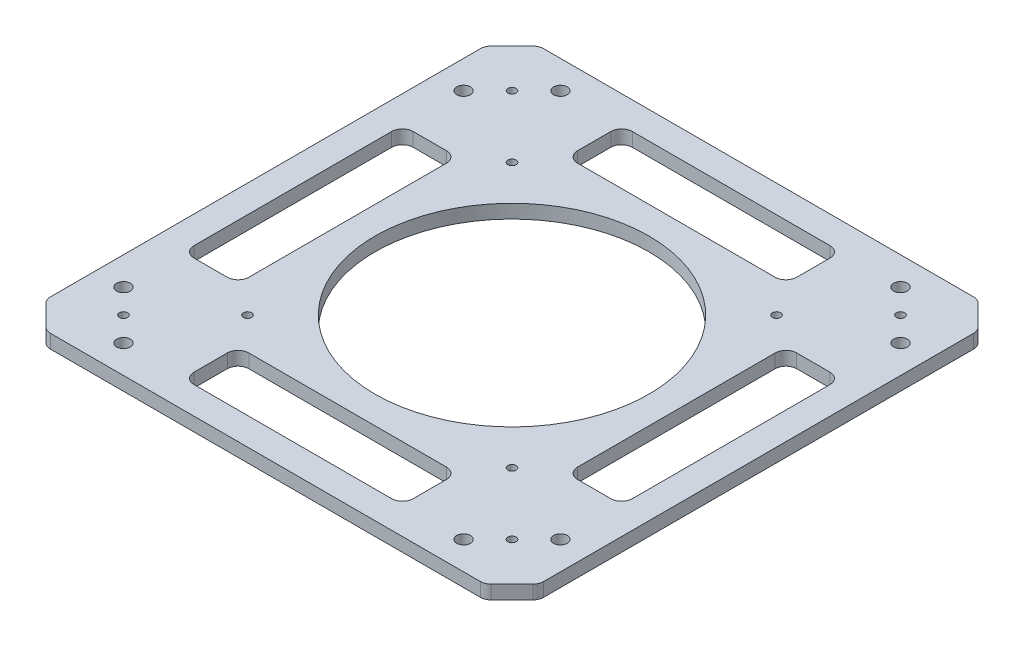
SolidWorks part; units mm, degrees
material "Hexcel AS4C (3000 Filaments)"
ref_plane "Front Plane" through (0, 0, 0) normal (0, 0, 1) x (1, 0, 0)
ref_plane "Top Plane" through (0, 0, 0) normal (0, 1, 0) x (1, 0, 0)
ref_plane "Right Plane" through (0, 0, 0) normal (1, 0, 0) x (0, 0, -1)
sketch "Sketch1" plane through (0, 0, 0) normal (0, 1, 0) x (1, 0, 0)
  line L0 (0, 0) -> (656.8243, 0) construction
  line L1 (0, 0) -> (0, 507.0819) construction
  line L2 (-203.454, 228.5987) -> (203.454, 228.5987)
  line L3 (203.454, 228.5987) -> (228.5987, 203.454)
  line L4 (228.5987, 203.454) -> (228.5987, -203.454)
  line L5 (203.454, -228.5987) -> (228.5987, -203.454)
  line L6 (-203.454, -228.5987) -> (203.454, -228.5987)
  line L7 (-203.454, -228.5987) -> (-228.5987, -203.454)
  line L8 (-228.5987, 203.454) -> (-228.5987, -203.454)
  line L9 (-203.454, 228.5987) -> (-228.5987, 203.454)
  point P4 (0, 0)
  point P11 (228.5987, 0)
  point P14 (0, -228.5987)
  point P17 (0, 228.5987)
  dimension "D1" = 203.454
  dimension "D2" = 35.56
  dimension "D3" = 45
extrude "Boss-Extrude1" add sketch "Sketch1" along normal blind 12.7
sketch "Sketch2" plane through (0, 12.7, 0) normal (0, 1, 0) x (1, 0, 0)
  line L0 (202.556, 157.6547) -> (221.4375, 176.5362) construction
  line L1 (0, 0) -> (0, 320.9857) construction
  line L2 (0, 0) -> (464.4972, 0) construction
  line L3 (122.6317, 122.6317) -> (180.1053, 180.1053) construction
  line L4 (118.1416, 127.1218) -> (175.6152, 184.5955)
  line L5 (127.1218, 118.1416) -> (184.5955, 175.6152)
  line L7 (-122.6317, 122.6317) -> (-180.1053, 180.1053) construction
  line L8 (-118.1416, 127.1218) -> (-175.6152, 184.5955)
  line L9 (-127.1218, 118.1416) -> (-184.5955, 175.6152)
  line L10 (-122.6317, -122.6317) -> (-180.1053, -180.1053) construction
  line L11 (-118.1416, -127.1218) -> (-175.6152, -184.5955)
  line L12 (-127.1218, -118.1416) -> (-184.5955, -175.6152)
  line L13 (122.6317, -122.6317) -> (180.1053, -180.1053) construction
  line L14 (118.1416, -127.1218) -> (175.6152, -184.5955)
  line L15 (127.1218, -118.1416) -> (184.5955, -175.6152)
  line L16 (0, 0) -> (244.2076, 244.2076) construction
  line L18 (228.5987, 203.454) -> (203.454, 228.5987) construction
  line L19 (180.1053, 180.1053) -> (202.556, 157.6547) construction
  arc A0 (118.1416, 127.1218) -> (127.1218, 118.1416) centre (122.6317, 122.6317) ccw
  arc A1 (184.5955, 175.6152) -> (175.6152, 184.5955) centre (180.1053, 180.1053) ccw
  arc A2 (-118.1416, 127.1218) -> (-127.1218, 118.1416) centre (-122.6317, 122.6317) cw
  arc A3 (-184.5955, 175.6152) -> (-175.6152, 184.5955) centre (-180.1053, 180.1053) cw
  arc A4 (-118.1416, -127.1218) -> (-127.1218, -118.1416) centre (-122.6317, -122.6317) ccw
  arc A5 (-184.5955, -175.6152) -> (-175.6152, -184.5955) centre (-180.1053, -180.1053) ccw
  arc A6 (118.1416, -127.1218) -> (127.1218, -118.1416) centre (122.6317, -122.6317) cw
  arc A7 (184.5955, -175.6152) -> (175.6152, -184.5955) centre (180.1053, -180.1053) cw
  circle A8 centre (202.556, 157.6547) radius 6.35
  circle A9 centre (157.6547, 202.556) radius 6.35
  circle A25 centre (-157.6547, 202.556) radius 6.35
  circle A32 centre (-202.556, 157.6547) radius 6.35
  circle A39 centre (-157.6547, -202.556) radius 6.35
  circle A47 centre (-202.556, -157.6547) radius 6.35
  circle A53 centre (157.6547, -202.556) radius 6.35
  circle A57 centre (202.556, -157.6547) radius 6.35
  circle A64 centre (0, 0) radius 127
  circle A73 centre (180.1053, 180.1053) radius 3.81
  circle A74 centre (122.6317, 122.6317) radius 3.81
  circle A75 centre (-180.1053, 180.1053) radius 3.81
  circle A76 centre (-122.6317, 122.6317) radius 3.81
  circle A77 centre (180.1053, -180.1053) radius 3.81
  circle A78 centre (122.6317, -122.6317) radius 3.81
  circle A79 centre (-122.6317, -122.6317) radius 3.81
  circle A80 centre (-180.1053, -180.1053) radius 3.81
  point P7 (151.3685, 151.3685)
  point P21 (-151.3685, 151.3685)
  point P28 (-151.3685, -151.3685)
  point P35 (151.3685, -151.3685)
  point P56 (202.556, 157.6547)
  dimension "D2" = 6.35
  dimension "D5" = 31.75
  dimension "D6" = 12.7
  dimension "D7" = 302.737
  dimension "D8" = 2.54
  dimension "D10" = 254
  dimension "D9" = 2.54
  dimension "D1" = 45
  dimension "D3" = 40.64
  dimension "D4" = 50.8
extrude "Cut-Extrude1" cut sketch "Sketch2" against normal through all both and the other way through all contours A25 | A32 | A47 | A57 | A9 | A8 | A78 | A77 | A79 | A80 | A75 | A76 | A73 | A64 | A74
sketch "Sketch3" plane through (0, 12.7, 0) normal (0, 1, 0) x (1, 0, 0)
  line L0 (0, 0) -> (320.2964, 0) construction
  line L1 (0, 0) -> (0, 272.5431) construction
  line L2 (228.5987, -203.454) -> (228.5987, 203.454) construction
  line L5 (152.3987, -101.6) -> (203.1987, -101.6)
  line L6 (152.3987, -101.6) -> (152.3987, 101.6)
  line L7 (152.3987, 101.6) -> (203.1987, 101.6)
  line L8 (203.1987, -101.6) -> (203.1987, 101.6)
  line L9 (152.3987, -101.6) -> (203.1987, 101.6) construction
  line L10 (152.3987, 101.6) -> (203.1987, -101.6) construction
  line L11 (101.6, -152.3987) -> (101.6, -203.1987)
  line L12 (-101.6, -152.3987) -> (101.6, -152.3987)
  line L13 (-101.6, -203.1987) -> (101.6, -203.1987)
  line L14 (-101.6, -152.3987) -> (-101.6, -203.1987)
  line L15 (-152.3987, -101.6) -> (-203.1987, -101.6)
  line L16 (-152.3987, 101.6) -> (-152.3987, -101.6)
  line L17 (-203.1987, 101.6) -> (-203.1987, -101.6)
  line L18 (-152.3987, 101.6) -> (-203.1987, 101.6)
  line L19 (-101.6, 152.3987) -> (-101.6, 203.1987)
  line L20 (101.6, 152.3987) -> (-101.6, 152.3987)
  line L21 (101.6, 203.1987) -> (-101.6, 203.1987)
  line L22 (101.6, 152.3987) -> (101.6, 203.1987)
  point P3 (177.7987, 0)
  point P26 (0, 0)
  dimension "D1" = 25.4
  dimension "D2" = 101.6
  dimension "D3" = 50.8
  dimension "D4" = 4
extrude "Cut-Extrude2" cut sketch "Sketch3" against normal through all both and the other way through all
fillet "Fillet1" radius 10 8 edges at (-228.5987, 6.35, 203.454) (-203.454, 6.35, 228.5987) (203.454, 6.35, 228.5987) (228.5987, 6.35, 203.454) (228.5987, 6.35, -203.454) (203.454, 6.35, -228.5987) (-203.454, 6.35, -228.5987) (-228.5987, 6.35, -203.454)
fillet "Fillet2" radius 10 16 edges at (-203.1987, 6.35, -101.6) (-152.3987, 6.35, -101.6) (-152.3987, 6.35, 101.6) (-203.1987, 6.35, 101.6) (-101.6, 6.35, 203.1987) (-101.6, 6.35, 152.3987) (101.6, 6.35, 203.1987) (101.6, 6.35, 152.3987) (203.1987, 6.35, -101.6) (203.1987, 6.35, 101.6) (152.3987, 6.35, 101.6) (152.3987, 6.35, -101.6) (101.6, 6.35, -152.3987) (101.6, 6.35, -203.1987) (-101.6, 6.35, -203.1987) (-101.6, 6.35, -152.3987)
scale "Scale1" scale about centroid uniform scaling yes scale factor 0.5
